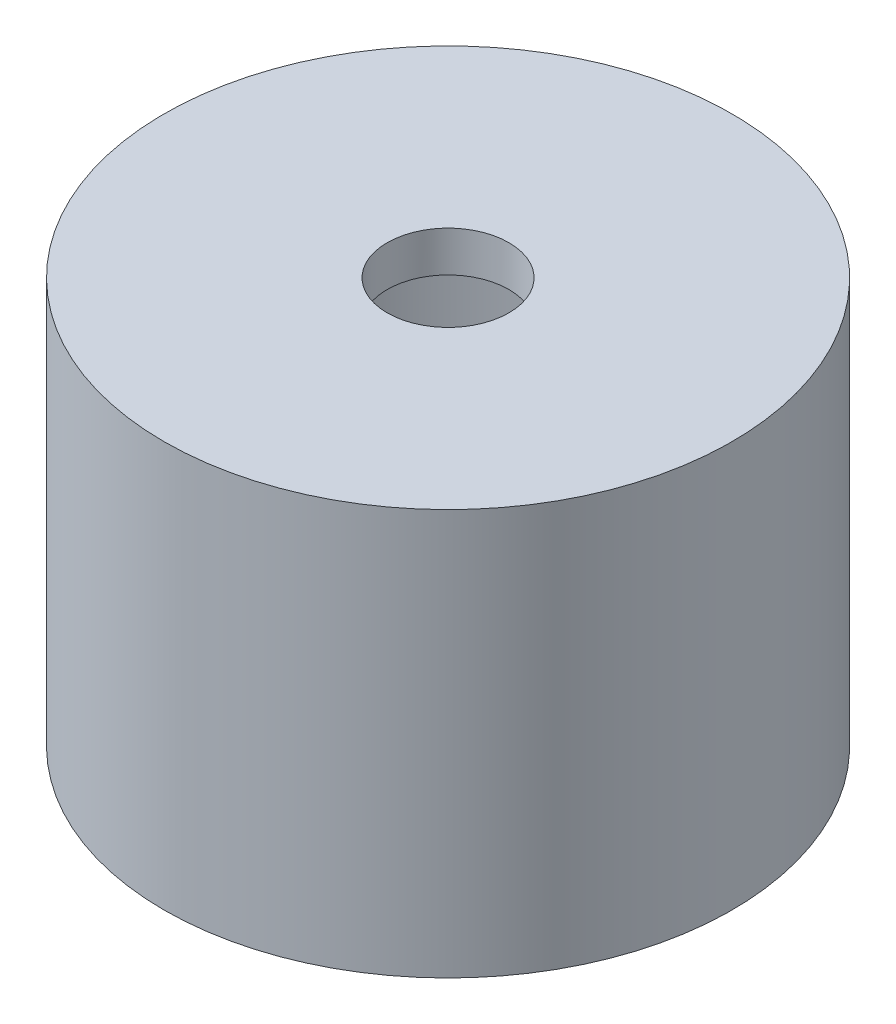
SolidWorks part; units mm, degrees
ref_plane "Ön Düzlem" through (0, 0, 0) normal (0, 0, 1) x (1, 0, 0)
ref_plane "Üst Düzlem" through (0, 0, 0) normal (0, 1, 0) x (1, 0, 0)
ref_plane "Sağ Düzlem" through (0, 0, 0) normal (1, 0, 0) x (0, 0, -1)
sketch "Sketch1" plane through (0, 0, 0) normal (0, 1, 0) x (1, 0, 0)
  circle A0 centre (0, 0) radius 7
  dimension "D1" = 14
extrude "Boss-Extrude1" add sketch "Sketch1" along normal blind 10
shell "Shell1" thickness 1
sketch "Sketch2" plane through (0, 9, 0) normal (0, -1, 0) x (-1, 0, 0)
  circle A0 centre (0, 0) radius 1.5
extrude "Cut-Extrude1" cut sketch "Sketch2" against normal blind 10
